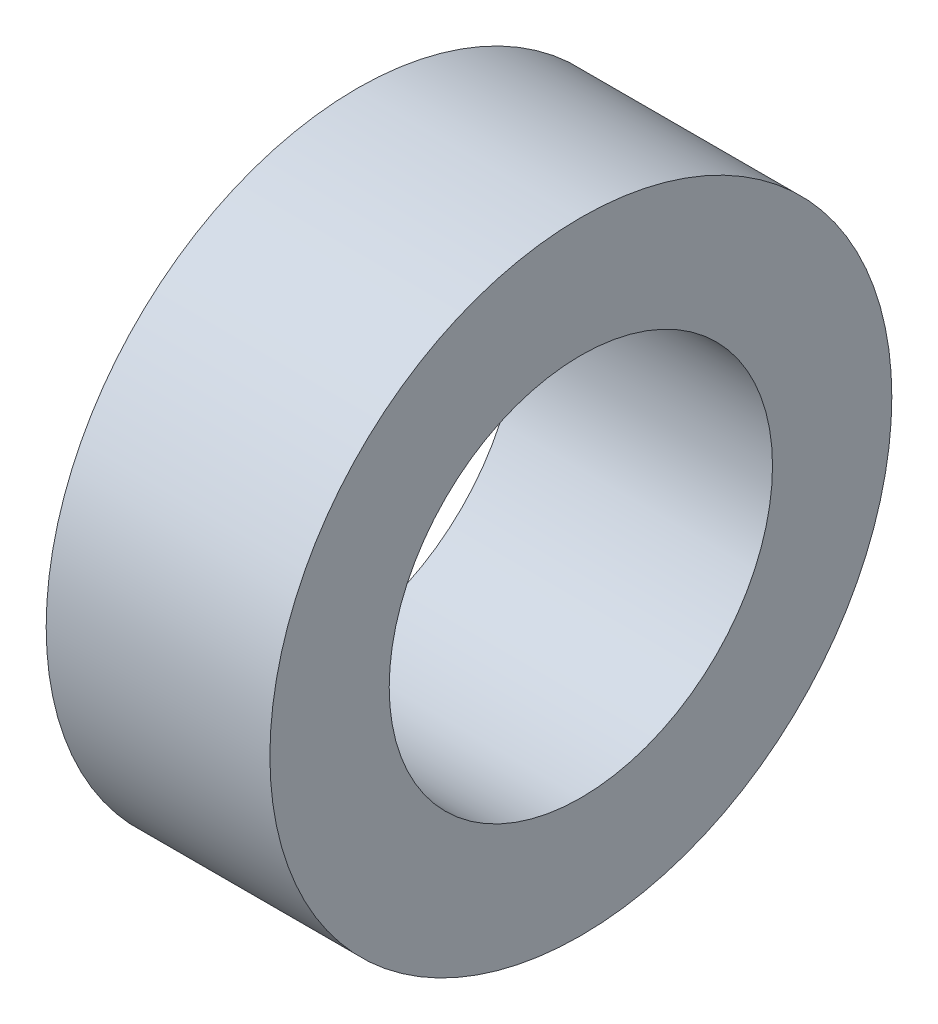
SolidWorks part; units mm, degrees
material "Nylon 101"
ref_plane "Front Plane" through (0, 0, 0) normal (0, 0, 1) x (1, 0, 0)
ref_plane "Top Plane" through (0, 0, 0) normal (0, 1, 0) x (1, 0, 0)
ref_plane "Right Plane" through (0, 0, 0) normal (1, 0, 0) x (0, 0, -1)
sketch "Sketch1" plane through (0, 0, 0) normal (1, 0, 0) x (0, 0, -1)
  circle A0 centre (0, 0) radius 10.2
  circle A1 centre (0, 0) radius 11.9011
  dimension "D1" = 20.4
  dimension "D2" = 23.8022
extrude "Boss-Extrude1" add sketch "Sketch1" along normal blind 13.55
sketch "Sketch2" plane through (13.55, 0, 0) normal (1, 0, 0) x (0, 0, -1)
  circle A0 centre (0, 0) radius 16.55
  circle A1 centre (0, 0) radius 10.2 construction
  circle A2 centre (0, 0) radius 10.2
  dimension "D1" = 6.35
extrude "Boss-Extrude2" add sketch "Sketch2" against normal blind 11.9062
equation "\"D2@Sketch1\"=11.9011mm*2"
equation "\"D1@Boss-Extrude1\"=13.55mm"
equation "\"D1@Boss-Extrude2\"=18.9mm-.25in"
